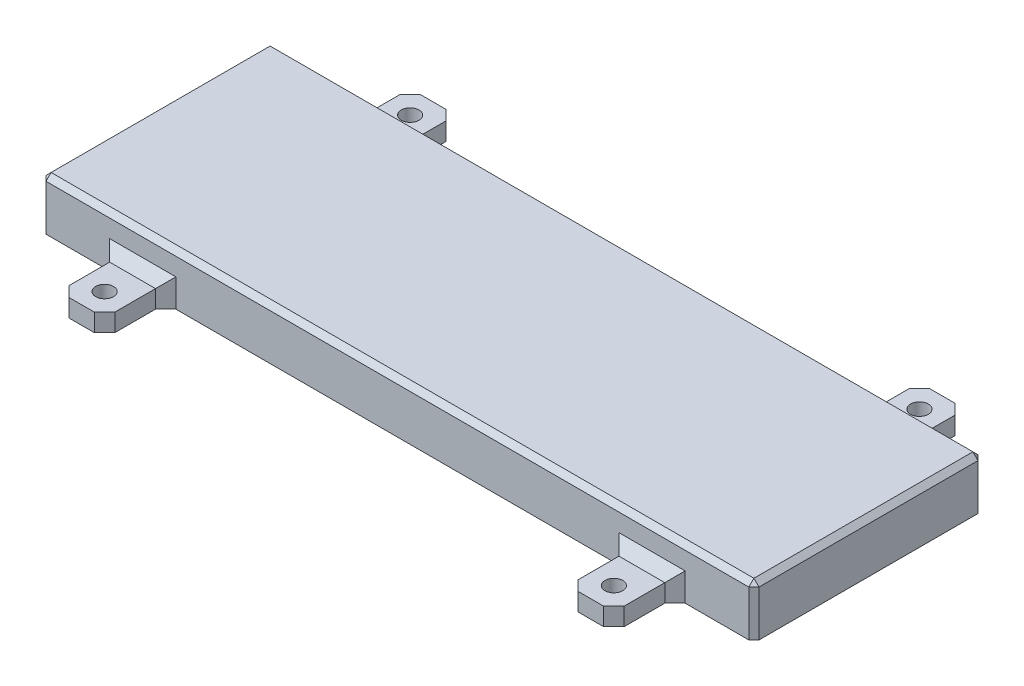
SolidWorks part; units mm, degrees
ref_plane "Alzado" through (0, 0, 0) normal (0, 0, 1) x (1, 0, 0)
ref_plane "Planta" through (0, 0, 0) normal (0, 1, 0) x (1, 0, 0)
ref_plane "Vista lateral" through (0, 0, 0) normal (1, 0, 0) x (0, 0, -1)
sketch "Croquis1" plane through (0, 0, 0) normal (0, 1, 0) x (1, 0, 0)
  line L1 (-68, -20.5) -> (68, -20.5)
  line L2 (-68, -20.5) -> (-68, 20.5)
  line L3 (-68, 20.5) -> (68, 20.5)
  line L4 (68, -20.5) -> (68, 20.5)
  line L5 (-68, -20.5) -> (68, 20.5) construction
  line L6 (-68, 20.5) -> (68, -20.5) construction
  line L7 (-70, -22.5) -> (70, -22.5)
  line L8 (-70, -22.5) -> (-70, 22.5)
  line L9 (-70, 22.5) -> (70, 22.5)
  line L10 (70, -22.5) -> (70, 22.5)
  line L11 (-70, -22.5) -> (70, 22.5) construction
  line L12 (-70, 22.5) -> (70, -22.5) construction
  point P0 (0, 0)
  point P6 (0, 0)
  dimension "D1" = 136
  dimension "D2" = 41
  dimension "D3" = 2
  dimension "D4" = 2
extrude "Saliente-Extruir1" add sketch "Croquis1" along normal blind 10
sketch "Croquis2" plane through (0, 10, 0) normal (0, 1, 0) x (1, 0, 0)
  line L1 (-70, 22.5) -> (70, 22.5)
  line L2 (-70, 22.5) -> (-70, -22.5)
  line L3 (-70, -22.5) -> (70, -22.5)
  line L4 (70, 22.5) -> (70, -22.5)
extrude "Saliente-Extruir2" add sketch "Croquis2" against normal blind 2
chamfer "Chaflán1" distance 1 angle 45 8 edges at (0, 10, 22.5) (70, 5, 22.5) (70, 10, 0) (70, 5, -22.5) (0, 10, -22.5) (-70, 5, -22.5) (-70, 10, 0) (-70, 5, 22.5)
sketch "Croquis3" plane through (0, 0, 0) normal (0, 1, 0) x (1, 0, 0)
  line L0 (-69, 22.5) -> (69, 22.5) construction
  line L1 (-54.5, 22.5) -> (-45.5, 22.5)
  line L2 (-54.5, 22.5) -> (-54.5, 34.5)
  line L3 (-54.5, 34.5) -> (-45.5, 34.5)
  line L4 (-45.5, 22.5) -> (-45.5, 34.5)
  line L5 (69, -22.5) -> (-69, -22.5) construction
  line L6 (45.5, 22.5) -> (54.5, 22.5)
  line L7 (45.5, 22.5) -> (45.5, 34.5)
  line L8 (45.5, 34.5) -> (54.5, 34.5)
  line L9 (54.5, 22.5) -> (54.5, 34.5)
  line L10 (-54.5, -22.5) -> (-45.5, -22.5)
  line L11 (-54.5, -22.5) -> (-54.5, -34.5)
  line L12 (-54.5, -34.5) -> (-45.5, -34.5)
  line L13 (-45.5, -22.5) -> (-45.5, -34.5)
  line L14 (-45.5, 34.5) -> (45.5, 34.5) construction
  line L15 (45.5, -22.5) -> (54.5, -22.5)
  line L16 (45.5, -22.5) -> (45.5, -34.5)
  line L17 (45.5, -34.5) -> (54.5, -34.5)
  line L18 (54.5, -22.5) -> (54.5, -34.5)
  line L19 (-45.5, -34.5) -> (45.5, -34.5) construction
  line L20 (-50, 30) -> (50, 30) construction
  line L21 (50, 30) -> (50, -30) construction
  line L22 (50, -30) -> (-50, -30) construction
  line L23 (-50, -30) -> (-50, 30) construction
  circle A0 centre (-50, 30) radius 1.75
  circle A1 centre (50, 30) radius 1.75
  circle A2 centre (-50, -30) radius 1.75
  circle A3 centre (50, -30) radius 1.75
  point P20 (0, -34.5)
  point P21 (0, 34.5)
  point P31 (-50, 0)
  point P32 (50, 0)
  point P33 (0, 30)
  point P34 (0, -30)
  point P36 (-50, -34.5)
  point P37 (50, -34.5)
  point P39 (50, 34.5)
  dimension "D3" = 3.5
  dimension "D1" = 100
  dimension "D2" = 60
  dimension "D4" = 9
  dimension "D5" = 12
extrude "Saliente-Extruir3" add sketch "Croquis3" along normal blind 3.5
chamfer "Chaflán2" distance 2 angle 45 20 edges at (54.5, 1.75, 34.5) (45.5, 1.75, 34.5) (-45.5, 1.75, 34.5) (-54.5, 1.75, 34.5) (-54.5, 1.75, -34.5) (-45.5, 1.75, -34.5) (54.5, 1.75, -34.5) (45.5, 1.75, -34.5) (45.5, 1.75, -22.5) (50, 3.5, -22.5) (54.5, 1.75, -22.5) (-45.5, 1.75, -22.5) (-54.5, 1.75, -22.5) (-50, 3.5, -22.5) (45.5, 1.75, 22.5) (54.5, 1.75, 22.5) (50, 3.5, 22.5) (-45.5, 1.75, 22.5) (-50, 3.5, 22.5) (-54.5, 1.75, 22.5)
sketch "Croquis4" plane through (-70, 0, 0) normal (-1, 0, 0) x (0, 0, 1)
  line L0 (-21.5, 0) -> (21.5, 0) construction
  line L1 (-10, 0) -> (10, 0)
  line L2 (-10, 0) -> (-10, 7.5)
  line L3 (-10, 7.5) -> (10, 7.5)
  line L4 (10, 0) -> (10, 7.5)
  point P6 (0, 7.5)
  dimension "D1" = 20
  dimension "D2" = 7.5
extrude "Cortar-Extruir1" cut sketch "Croquis4" against normal blind 3.5
